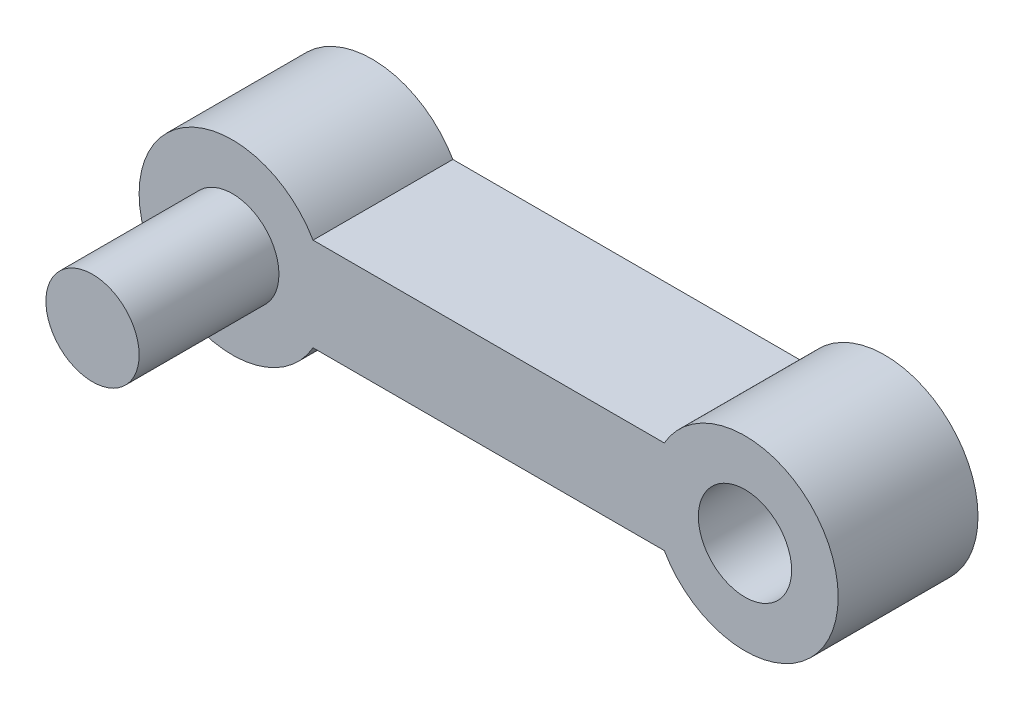
SolidWorks part; units mm, degrees
ref_plane "Спереди" through (0, 0, 0) normal (0, 0, 1) x (1, 0, 0)
ref_plane "Сверху" through (0, 0, 0) normal (0, 1, 0) x (1, 0, 0)
ref_plane "Справа" through (0, 0, 0) normal (1, 0, 0) x (0, 0, -1)
other "Configuration Table"
sketch "Sketch2" plane through (0, 0, 0) normal (0, 0, 1) x (1, 0, 0)
  line L1 (-36.505, 13.8003) -> (-28.9691, 13.8003)
  line L5 (-36.505, 11.8003) -> (-28.9691, 11.8003)
  line L7 (-13.5959, 12.8003) -> (-45.3291, 12.8003) construction
  arc A0 (-36.505, 13.8003) -> (-36.505, 11.8003) centre (-38.2371, 12.8003) ccw
  arc A2 (-28.9691, 13.8003) -> (-28.9691, 11.8003) centre (-27.2371, 12.8003) cw
  arc A3 (-36.505, 11.8003) -> (-36.2371, 12.8003) centre (-38.2371, 12.8003) ccw construction
  arc A4 (-36.2371, 12.8003) -> (-36.505, 13.8003) centre (-38.2371, 12.8003) ccw construction
  arc A5 (-28.9691, 11.8003) -> (-29.2371, 12.8003) centre (-27.2371, 12.8003) cw construction
  arc A6 (-29.2371, 12.8003) -> (-28.8371, 14.0003) centre (-27.2371, 12.8003) cw construction
  dimension "D3" = 4
  dimension "D1" = 2
  dimension "D2" = 11
extrude "Boss-Extrude1" add sketch "Sketch2" along normal blind 3
ref_plane "Plane1" through (0, 0, 3) normal (0, 0, 1) x (1, 0, 0)
sketch "Sketch3" plane through (0, 0, 3) normal (0, 0, 1) x (1, 0, 0)
  circle A0 centre (-38.2371, 12.8003) radius 1
  dimension "D1" = 2
extrude "Boss-Extrude2" add sketch "Sketch3" along normal blind 3
ref_plane "Plane2" through (0, 0, 0) normal (0, 0, -1) x (-1, 0, 0)
sketch "Sketch4" plane through (0, 0, 0) normal (0, 0, -1) x (-1, 0, 0)
  circle A0 centre (27.2371, 12.8003) radius 1
  circle A1 centre (38.2371, 12.8003) radius 1 construction
extrude "Cut-Extrude1" cut sketch "Sketch4" against normal up to surface (3 mm away) up to face at (-37.2371, 12.8003, 3)
equation "\"R small\"= 2"
equation "\"R big\"= 4"
equation "\"width\"= 0.6"
equation "\"border width\"= 1"
equation "\"D3@Sketch2\"=\"R big\""
equation "\"D1@Sketch2\"=\"R small\""
equation "\"D1@Sketch3\"=\"R small\""
